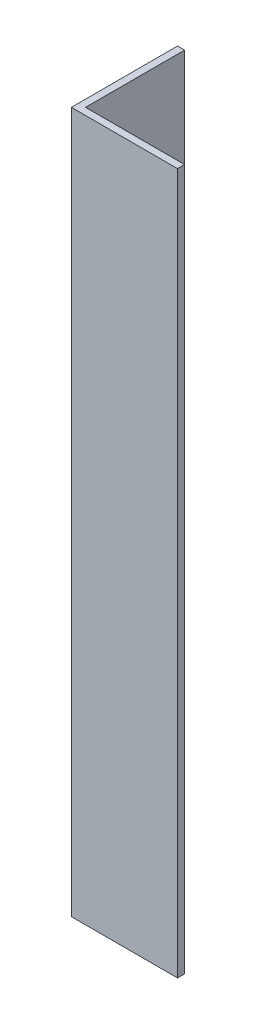
SolidWorks part; units mm, degrees
material "1060 Сплав"
ref_plane "Спереди" through (0, 0, 0) normal (0, 0, 1) x (1, 0, 0)
ref_plane "Сверху" through (0, 0, 0) normal (0, 1, 0) x (1, 0, 0)
ref_plane "Справа" through (0, 0, 0) normal (1, 0, 0) x (0, 0, -1)
sketch "Эскиз1" plane through (0, 0, 0) normal (0, 1, 0) x (1, 0, 0)
  line L0 (0, 0) -> (0, 15)
  line L1 (0, 15) -> (1, 15)
  line L2 (1, 15) -> (1, 1)
  line L3 (1, 1) -> (15, 1)
  line L4 (15, 1) -> (15, 0)
  line L5 (15, 0) -> (0, 0)
  dimension "D1" = 1
  dimension "D2" = 15
extrude "Бобышка-Вытянуть1" add sketch "Эскиз1" along normal blind 99
